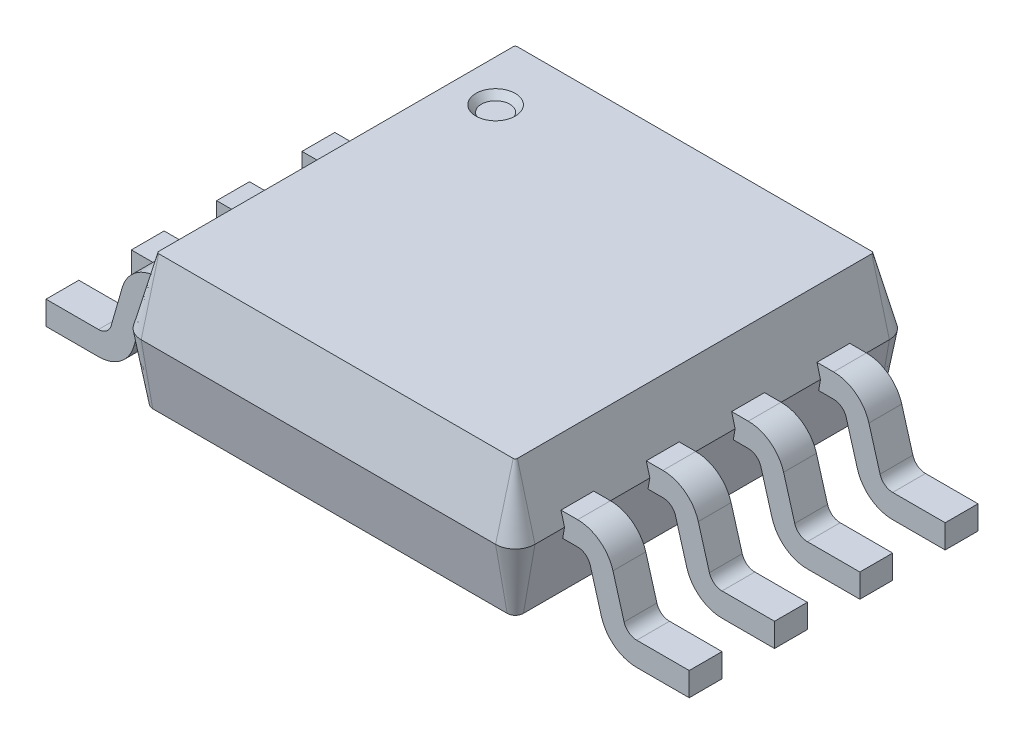
SolidWorks part; units mm, degrees
other "Camera1"
ref_plane "Front" through (0, 0, 0) normal (0, 0, 1) x (1, 0, 0)
ref_plane "Top" through (0, 0, 0) normal (0, 1, 0) x (1, 0, 0)
ref_plane "Right" through (0, 0, 0) normal (1, 0, 0) x (0, 0, -1)
sketch "Sketch1" plane through (0, 0, 0) normal (0, 1, 0) x (1, 0, 0)
  line L0 (-1.35, 1.35) -> (1.35, -1.35) construction
  line L1 (-1.35, 1.5) -> (1.35, 1.5)
  line L2 (-1.5, 1.35) -> (-1.5, -1.35)
  line L3 (-1.35, -1.5) -> (1.35, -1.5)
  line L4 (1.5, 1.35) -> (1.5, -1.35)
  arc A0 (-1.5, 1.35) -> (-1.35, 1.5) centre (-1.35, 1.35) cw
  arc A1 (1.5, 1.35) -> (1.35, 1.5) centre (1.35, 1.35) ccw
  arc A2 (1.35, -1.5) -> (1.5, -1.35) centre (1.35, -1.35) ccw
  arc A3 (-1.5, -1.35) -> (-1.35, -1.5) centre (-1.35, -1.35) ccw
  point P0 (0, 0)
  dimension "D1" = 0.15
  dimension "D2" = 0.15
  dimension "D3" = 0.15
  dimension "D4" = 0.15
  dimension "D5" = 3
  dimension "D6" = 3
extrude "Extrude1" add sketch "Sketch1" along normal blind 0.5 draft 15 and the other way blind 0.5 draft 10 from offset 0.65
sketch "Sketch2" plane through (0, 1.15, 0) normal (0, 1, 0) x (1, 0, 0)
  circle A0 centre (-1.05, 0.9) radius 0.15
sketch "Sketch3" plane through (0, 0, 0) normal (0, 0, 1) x (1, 0, 0)
  line L0 (-2.45, 0) -> (-2.05, 0)
  line L1 (1.45, 0.75) -> (1.6, 0.75)
  line L2 (1.45, 0.57) -> (1.45, 0.75)
  line L3 (2.45, 0.18) -> (2.05, 0.18)
  line L4 (2.45, 0) -> (2.45, 0.18)
  line L5 (1.45, 0.57) -> (1.6, 0.57)
  line L6 (0, 0.15) -> (0, 1.15) construction
  line L7 (1.6961, 0.4976) -> (1.7809, 0.2026)
  line L8 (-1.35, 0.15) -> (1.35, 0.15) construction
  line L9 (1.8691, 0.5474) -> (1.9539, 0.2524)
  line L10 (-1.35, 1.15) -> (1.35, 1.15) construction
  line L11 (2.45, 0) -> (2.05, 0)
  line L27 (-1.8691, 0.5474) -> (-1.9539, 0.2524)
  line L28 (-1.6961, 0.4976) -> (-1.7809, 0.2026)
  line L29 (-1.45, 0.57) -> (-1.6, 0.57)
  line L30 (-2.45, 0) -> (-2.45, 0.18)
  line L31 (-2.45, 0.18) -> (-2.05, 0.18)
  line L32 (-1.45, 0.57) -> (-1.45, 0.75)
  line L33 (-1.45, 0.75) -> (-1.6, 0.75)
  arc A0 (1.9539, 0.2524) -> (2.05, 0.18) centre (2.05, 0.28) ccw
  arc A1 (1.6961, 0.4976) -> (1.6, 0.57) centre (1.6, 0.47) ccw
  arc A2 (1.7809, 0.2026) -> (2.05, 0) centre (2.05, 0.28) ccw
  arc A3 (1.8691, 0.5474) -> (1.6, 0.75) centre (1.6, 0.47) ccw
  arc A12 (-1.8691, 0.5474) -> (-1.6, 0.75) centre (-1.6, 0.47) cw
  arc A13 (-1.7809, 0.2026) -> (-2.05, 0) centre (-2.05, 0.28) cw
  arc A14 (-1.6961, 0.4976) -> (-1.6, 0.57) centre (-1.6, 0.47) cw
  arc A15 (-1.9539, 0.2524) -> (-2.05, 0.18) centre (-2.05, 0.28) cw
  dimension "D1" = 0.45
  dimension "D2" = 0.75
  dimension "D3" = 0.18
  dimension "D4" = 0.28
  dimension "D5" = 0.4
  dimension "D6" = 1
  dimension "D7" = 2.45
extrude "ICE1" add sketch "Sketch3" along normal blind 0.125 and the other way blind 0.125 from offset 1
pattern_linear "LPattern1" count 4 spacing 0.65 along (0, 0, -1) of "ICE1"
extrude "ICE2" cut sketch "Sketch2" against normal blind 0.05 draft 40
